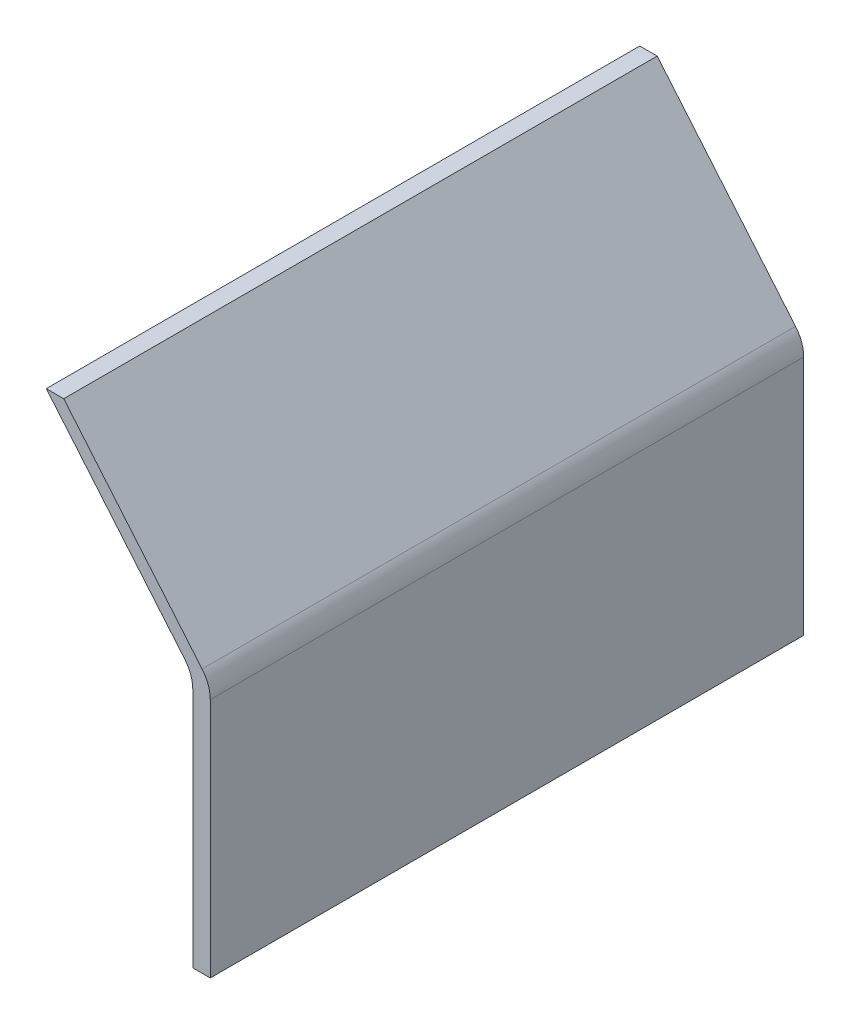
SolidWorks part; units mm, degrees
material "201 Annealed Stainless Steel (SS)"
ref_plane "Front Plane" through (0, 0, 0) normal (0, 0, 1) x (1, 0, 0)
ref_plane "Top Plane" through (0, 0, 0) normal (0, 1, 0) x (1, 0, 0)
ref_plane "Right Plane" through (0, 0, 0) normal (1, 0, 0) x (0, 0, -1)
sketch "Sketch1" plane through (0, 0, 0) normal (0, 0, 1) x (1, 0, 0)
  line L0 (0, 0) -> (-5, 0)
  line L1 (-5, 0) -> (-5, 72.7)
  line L2 (-5, 72.7) -> (-46.974, 122.7227)
  line L3 (-46.974, 122.7227) -> (-41.974, 122.7227)
  line L4 (-41.974, 122.7227) -> (0, 72.7)
  line L5 (0, 72.7) -> (0, 0)
  dimension "D1" = 5
  dimension "D2" = 5
  dimension "D3" = 72.7
  dimension "D4" = 140
  dimension "D5" = 65.3
extrude "Funnel - Left Side" add sketch "Sketch1" along normal blind 170
fillet "Fillet1" radius 10 2 edges at (0, 72.7, 85) (-5, 72.7, 85)
